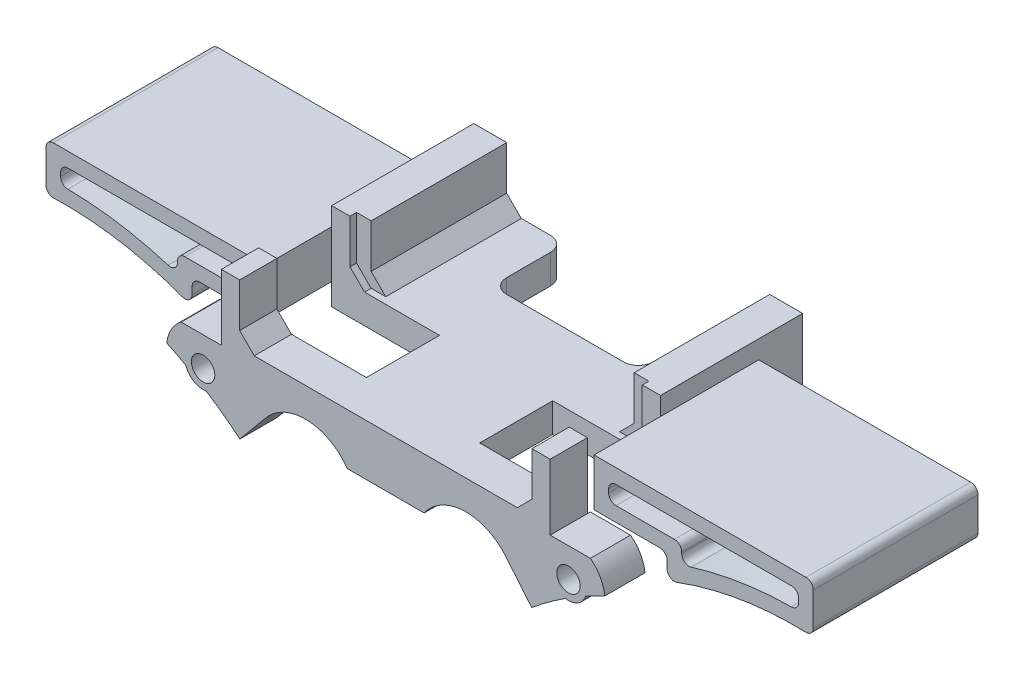
SolidWorks part; units mm, degrees
ref_plane "前视基准面" through (0, 0, 0) normal (0, 0, 1) x (1, 0, 0)
ref_plane "上视基准面" through (0, 0, 0) normal (0, 1, 0) x (1, 0, 0)
ref_plane "右视基准面" through (0, 0, 0) normal (1, 0, 0) x (0, 0, -1)
sketch "草图1" plane through (0, 0, 0) normal (0, 0, 1) x (1, 0, 0)
  line L0 (0, 0) -> (22.5, 0)
  line L1 (22.5, 0) -> (22.5, 12)
  line L2 (22.5, 12) -> (-22.5, 12)
  line L3 (-22.5, 12) -> (-22.5, 0)
  line L4 (-22.5, 0) -> (0, 0)
extrude "凸台-拉伸1" add sketch "草图1" along normal blind 34.55
sketch "草图2" plane through (0, 0, 34.55) normal (0, 0, 1) x (1, 0, 0)
  line L0 (-20, 12) -> (20, 12)
  line L1 (22.5, 12) -> (-22.5, 12) construction
  line L2 (20, 12) -> (20, 4)
  line L3 (20, 4) -> (-20, 4)
  line L4 (0, -6.6) -> (0, 6.6) construction
  line L5 (-20, 12) -> (-20, 4)
  point P9 (0, 4)
  point P10 (0, 12)
extrude "切除-拉伸1" cut sketch "草图2" against normal blind 16
chamfer "倒角1" distance 2 angle 45 2 edges at (20, 4, 26.55) (-20, 4, 26.55)
sketch "草图6" plane through (0, 12, 0) normal (0, 1, 0) x (1, 0, 0)
  line L0 (22.5, 0) -> (22.5, -13.5)
  line L2 (22.5, -34.55) -> (22.5, 0) construction
  line L3 (22.5, -13.5) -> (17, -13.5)
  line L4 (14.5, -11) -> (14.5, -5)
  line L5 (14.5, -5) -> (14.5, 0)
  line L6 (22.5, 0) -> (-22.5, 0) construction
  line L7 (14.5, 0) -> (22.5, 0)
  line L8 (0, -10.45) -> (0, 10.45) construction
  line L9 (-14.5, 0) -> (-22.5, 0)
  line L10 (-14.5, -5) -> (-14.5, 0)
  line L11 (-14.5, -11) -> (-14.5, -5)
  line L12 (-22.5, -13.5) -> (-17, -13.5)
  line L13 (-22.5, 0) -> (-22.5, -13.5)
  circle A0 centre (17, -5) radius 1.6
  circle A1 centre (17, -11) radius 1.6
  arc A2 (17, -13.5) -> (14.5, -11) centre (17, -11) cw
  arc A3 (-17, -13.5) -> (-14.5, -11) centre (-17, -11) ccw
  circle A4 centre (-17, -11) radius 1.6
  circle A5 centre (-17, -5) radius 1.6
extrude "凸台-拉伸2" add sketch "草图6" against normal blind 6.9
sketch "草图8" plane through (0, 0, 34.55) normal (0, 0, 1) x (1, 0, 0)
  line L1 (1.843, -25.3671) -> (9.2306, -19.6151)
  line L2 (-18, 4) -> (18, 4) construction
  line L3 (0, -10.45) -> (0, 10.45) construction
  line L5 (16.5232, -2.6996) -> (19.968, -6.8465)
  line L6 (-1.843, -25.3671) -> (-9.2306, -19.6151)
  line L7 (-5.4768, -11.3004) -> (-10.4216, -17.6514)
  line L8 (5.4768, -11.3004) -> (10.4216, -17.6514)
  line L9 (-16.5232, -2.6996) -> (-19.968, -6.8465)
  line L10 (22.5, 3) -> (22.5, 4)
  line L11 (-22.5, 12) -> (-22.5, 0) construction
  line L12 (-22.5, 3) -> (-28, 3)
  line L13 (-22.5, 3) -> (-22.5, 4)
  line L14 (22.5, 3) -> (28, 3)
  line L15 (-22.5, 4) -> (22.5, 4)
  circle A1 centre (25, -1) radius 1.6
  circle A3 centre (0, -23) radius 1.6
  arc A4 (-1.843, -25.3671) -> (1.843, -25.3671) centre (0, -23) ccw
  circle A6 centre (-25, -1) radius 1.6
  arc A8 (29.9729, -0.4804) -> (27.3654, -1.8093) centre (50, -43) ccw
  arc A9 (10.4216, -17.6514) -> (9.2306, -19.6151) centre (50, -43) ccw
  arc A10 (16.5232, -2.6996) -> (5.4768, -11.3004) centre (11, -7) ccw
  arc A11 (24.5837, -3.4651) -> (27.3654, -1.8093) centre (25, -1) ccw
  arc A12 (24.5837, -3.4651) -> (19.968, -6.8465) centre (50, -43) ccw
  arc A13 (-10.4216, -17.6514) -> (-9.2306, -19.6151) centre (-50, -43) cw
  arc A14 (-16.5232, -2.6996) -> (-5.4768, -11.3004) centre (-11, -7) cw
  arc A15 (-24.5837, -3.4651) -> (-19.968, -6.8465) centre (-50, -43) cw
  arc A16 (-24.5837, -3.4651) -> (-27.3654, -1.8093) centre (-25, -1) cw
  arc A17 (-29.9729, -0.4804) -> (-27.3654, -1.8093) centre (-50, -43) cw
  arc A18 (-29.9729, -0.4804) -> (-28, 3) centre (-25, -1) cw
  arc A19 (29.9729, -0.4804) -> (28, 3) centre (25, -1) ccw
  point P23 (0, 4)
extrude "凸台-拉伸3" add sketch "草图8" against normal blind 5.5
sketch "草图11" plane through (0, 0, 29.05) normal (0, 0, -1) x (-1, 0, 0)
  line L1 (-4, -7) -> (-10.4216, -17.6514)
  line L2 (-10.4216, -17.6514) -> (-10.4216, -27.0892)
  line L3 (-10.4216, -27.0892) -> (10.4216, -27.0892)
  line L4 (0, 19.0025) -> (0, -19.0025) construction
  line L5 (10.4216, -17.6514) -> (10.4216, -27.0892)
  line L6 (4, -7) -> (10.4216, -17.6514)
  line L8 (0, -3) -> (5.2554, -3)
  line L9 (0, -3) -> (-5.2554, -3)
  line L10 (-5.2554, -3) -> (-4, -7)
  line L11 (5.2554, -3) -> (4, -7)
  arc A0 (-5.4768, -11.3004) -> (-11, 0) centre (-11, -7) ccw construction
  arc A1 (11, 0) -> (5.4768, -11.3004) centre (11, -7) ccw construction
  point P16 (0, -27.0892)
extrude "切除-拉伸6" cut sketch "草图11" against normal blind 10
sketch "草图12" plane through (0, 0, 18.55) normal (0, 0, 1) x (1, 0, 0)
  line L0 (-18, 6) -> (-16, 4)
  line L1 (20, 12) -> (-20, 12) construction
  line L4 (-18, 6) -> (-18, 12)
  line L5 (-18, 4) -> (18, 4) construction
  line L6 (-16, 4) -> (16, 4)
  line L7 (-18, 4) -> (18, 4) construction
  line L8 (0, -19.0025) -> (0, 19.0025) construction
  line L9 (18, 6) -> (18, 12)
  line L10 (18, 6) -> (16, 4)
  line L11 (-18, 12) -> (18, 12)
  point P15 (0, 4)
extrude "切除-拉伸7" cut sketch "草图12" against normal blind 25
sketch "草图13" plane through (0, 4, 0) normal (0, 1, 0) x (1, 0, 0)
  line L9 (-22.5, -34.55) -> (-22.5, 0) construction
  line L11 (-7.75, -24.45) -> (-7.75, -28.45)
  line L12 (-22.5, -24.45) -> (-22.5, -28.45)
  line L18 (-7.75, -28.45) -> (-7.75, -29.45)
  line L19 (-7.75, -29.45) -> (-22.5, -29.45)
  line L20 (-22.5, -29.05) -> (-22.5, -34.55) construction
  line L21 (-22.5, -29.45) -> (-22.5, -28.45)
  line L24 (-22.5, -21.45) -> (-22.5, -24.45)
  line L34 (-7.75, -24.45) -> (-7.75, -19.45)
  line L35 (-7.75, -19.45) -> (-22.5, -19.45)
  line L36 (-22.5, -19.45) -> (-22.5, -21.45)
  line L37 (0, -19.0025) -> (0, 19.0025) construction
  line L38 (22.5, -19.45) -> (22.5, -21.45)
  line L39 (7.75, -19.45) -> (22.5, -19.45)
  line L40 (7.75, -24.45) -> (7.75, -19.45)
  line L41 (22.5, -21.45) -> (22.5, -24.45)
  line L42 (22.5, -29.45) -> (22.5, -28.45)
  line L43 (7.75, -29.45) -> (22.5, -29.45)
  line L44 (7.75, -28.45) -> (7.75, -29.45)
  line L45 (22.5, -24.45) -> (22.5, -28.45)
  line L46 (7.75, -24.45) -> (7.75, -28.45)
extrude "切除-拉伸8" cut sketch "草图13" against normal blind 25 and the other way blind 25
sketch "草图14" plane through (0, 4, 0) normal (0, 1, 0) x (1, 0, 0)
  line L1 (-10, -10) -> (10, -10)
  line L2 (10, -10) -> (10, 0)
  line L3 (-16, 0) -> (16, 0) construction
  line L4 (10, 0) -> (-10, 0)
  line L5 (-10, -10) -> (-10, 0)
extrude "切除-拉伸9" cut sketch "草图14" against normal blind 25
fillet "圆角1" radius 2 4 edges at (-10, 2, 0) (10, 2, 0) (10, 2, 10) (-10, 2, 10)
sketch "草图15" plane through (0, 0, 0) normal (0, 0, -1) x (-1, 0, 0)
  line L0 (0, 19.0025) -> (0, -19.0025) construction
  line L1 (-22.5, 0) -> (-22.5, 12) construction
  line L2 (-22.5, 9.5) -> (-22.5, 3)
  line L3 (-22.5, 3) -> (-32.5, 3)
  line L4 (-22.5, 9.5) -> (-52.5, 9.5)
  line L5 (-52.5, 9.5) -> (-52.5, 2.932)
  line L6 (-32.5, 3) -> (-32.5, -0.4588)
  line L7 (24.5, 7.5) -> (50.5, 7.5)
  line L8 (-24.5, 7.5) -> (-24.5, 5)
  line L9 (-24.5, 5) -> (-34.5, 5)
  line L10 (-34.5, 5) -> (-34.5, 2.4285)
  line L11 (-50.5, 7.5) -> (-50.5, 4.9974)
  line L12 (-24.5, 7.5) -> (-50.5, 7.5)
  line L13 (50.5, 7.5) -> (50.5, 4.9974)
  line L14 (34.5, 5) -> (34.5, 2.4285)
  line L15 (24.5, 5) -> (34.5, 5)
  line L16 (24.5, 7.5) -> (24.5, 5)
  line L17 (32.5, 3) -> (32.5, -0.4588)
  line L18 (52.5, 9.5) -> (52.5, 2.932)
  line L19 (22.5, 9.5) -> (52.5, 9.5)
  line L20 (22.5, 3) -> (32.5, 3)
  line L21 (22.5, 9.5) -> (22.5, 3)
  arc A0 (-32.5, -0.4588) -> (-52.5, 2.932) centre (-50, -43) ccw
  arc A1 (-34.5, 2.4285) -> (-50.5, 4.9974) centre (-50, -43) ccw
  arc A2 (34.5, 2.4285) -> (50.5, 4.9974) centre (50, -43) cw
  arc A3 (32.5, -0.4588) -> (52.5, 2.932) centre (50, -43) cw
  dimension "D1" = 2
extrude "凸台-拉伸4" add sketch "草图15" against normal blind 22.55 from offset 6 offset against normal yes
fillet "圆角2" radius 1 20 edges at (-24.5, 5, 17.275) (-24.5, 7.5, 17.275) (-34.5, 5, 17.275) (-34.5, 2.4285, 17.275) (-50.5, 4.9974, 17.275) (-50.5, 7.5, 17.275) (-52.5, 9.5, 17.275) (-52.5, 2.932, 17.275) (-32.5, -0.4588, 17.275) (-32.5, 3, 17.275) (32.5, 3, 17.275) (52.5, 2.932, 17.275) (52.5, 9.5, 17.275) (50.5, 4.9974, 17.275) (50.5, 7.5, 17.275) (24.5, 7.5, 17.275) (24.5, 5, 17.275) (34.5, 5, 17.275) (34.5, 2.4285, 17.275) (32.5, -0.4588, 17.275)
